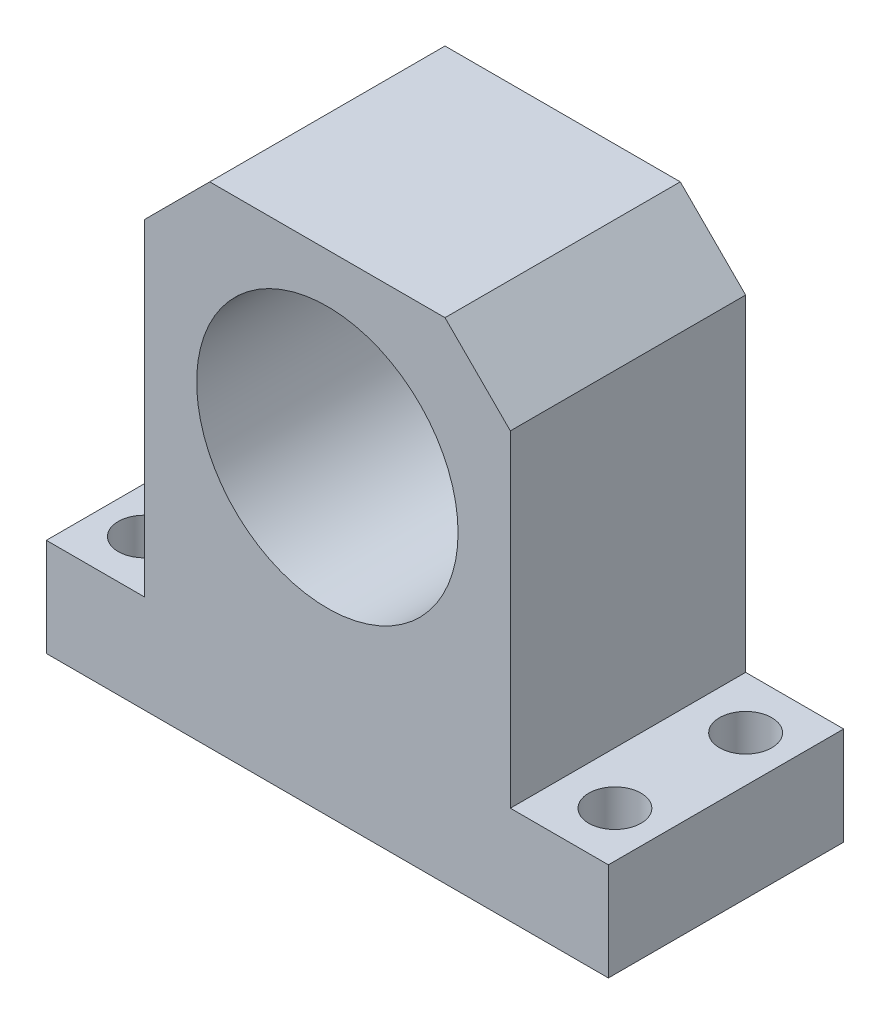
SolidWorks part; units mm, degrees
ref_plane "Płaszczyzna przednia" through (0, 0, 0) normal (0, 0, 1) x (1, 0, 0)
ref_plane "Płaszczyzna górna" through (0, 0, 0) normal (0, 1, 0) x (1, 0, 0)
ref_plane "Płaszczyzna prawa" through (0, 0, 0) normal (1, 0, 0) x (0, 0, -1)
sketch "Szkic1" plane through (0, 0, 0) normal (0, 0, 1) x (1, 0, 0)
  line L0 (0, 0) -> (86, 0)
  line L1 (86, 0) -> (86, 15)
  line L2 (86, 15) -> (71, 15)
  line L3 (71, 15) -> (71, 75)
  line L4 (71, 75) -> (15, 75)
  line L5 (15, 75) -> (15, 15)
  line L6 (15, 15) -> (0, 15)
  line L7 (0, 15) -> (0, 0)
  dimension "D1" = 86
  dimension "D2" = 15
  dimension "D3" = 15
  dimension "D4" = 60
  dimension "D5" = 56
extrude "Dodanie-wyciągnięcie1" add sketch "Szkic1" along normal blind 36
sketch "Szkic2" plane through (0, 0, 36) normal (0, 0, 1) x (1, 0, 0)
  line L0 (0, 0) -> (86, 0) construction
  line L1 (71, 75) -> (15, 75) construction
  line L4 (71, 75) -> (15, 75) construction
  circle A0 centre (43, 47.5) radius 20
  point P10 (43, 75)
  dimension "D1" = 47.5
  dimension "D4" = 40
  dimension "D2" = 27.5
extrude "Wytnij-wyciągnięcie1" cut sketch "Szkic2" against normal blind 36
chamfer "Sfazowanie1" distance 10 angle 45 2 edges at (71, 75, 18) (15, 75, 18)
sketch "Szkic3" plane through (0, 15, 0) normal (0, 1, 0) x (1, 0, 0)
  line L0 (0, -36) -> (0, 0) construction
  line L1 (86, -36) -> (86, 0) construction
  line L2 (86, 0) -> (71, 0) construction
  line L3 (86, -36) -> (71, -36) construction
  circle A0 centre (79, -8) radius 4
  circle A1 centre (7, -8) radius 4
  circle A2 centre (79, -28) radius 4
  circle A3 centre (7, -28) radius 4
  point P14 (0, 0)
  point P15 (0, 0)
  dimension "D1" = 8
  dimension "D5" = 8
  dimension "D6" = 8
  dimension "D8" = 8
  dimension "D2" = 7
  dimension "D3" = 7
  dimension "D4" = 8
  dimension "D7" = 8
extrude "Wytnij-wyciągnięcie2" cut sketch "Szkic3" against normal blind 18
